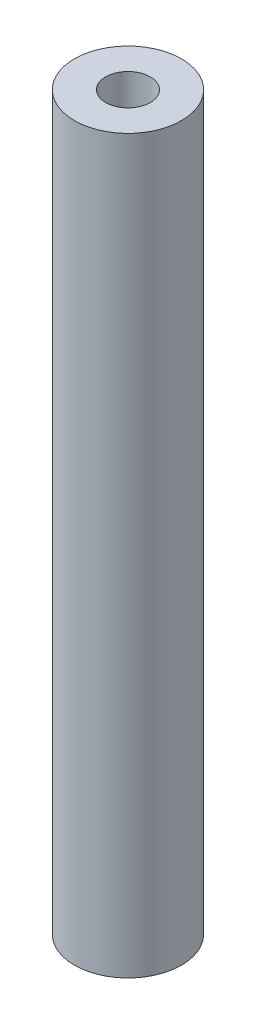
SolidWorks part; units mm, degrees
material "6061 合金"
ref_plane "前视基准面" through (0, 0, 0) normal (0, 0, 1) x (1, 0, 0)
ref_plane "上视基准面" through (0, 0, 0) normal (0, 1, 0) x (1, 0, 0)
ref_plane "右视基准面" through (0, 0, 0) normal (1, 0, 0) x (0, 0, -1)
sketch "草图1" plane through (0, 0, 0) normal (0, 1, 0) x (1, 0, 0)
  circle A0 centre (0, 0) radius 3
  dimension "D1" = 6
extrude "凸台-拉伸1" add sketch "草图1" along normal blind 41
sketch "草图2" plane through (0, 41, 0) normal (0, 1, 0) x (1, 0, 0)
  point P0 (0, 0)
hole_wizard "M3 螺纹孔1" positions "3D草图2" profile "草图3" tap size "M3" standard "GB"
sketch3d "3D草图2"
  point P0 (0, 41, 0)
sketch "草图3" plane through (0, 41, 0) normal (1, 0, 0) x (0, 0, 1)
  line L0 (0, 0) -> (0, 9.2511)
  line L1 (0, 9.2511) -> (1.25, 8.5)
  line L2 (1.25, 8.5) -> (1.25, 0)
  line L5 (1.25, 0) -> (0, 0)
  line L10 (0, 9.2511) -> (-1.25, 8.5) construction
  line L11 (0, -6.35) -> (0, 107.95) construction
  dimension "螺纹孔钻头直径" = 2.5
  dimension "螺纹孔钻头深度" = 8.5
  dimension "导头角度" = 118
cosmetic thread "孔螺蚊线1" parameters "D1"=6, "D2"=3
sketch "草图4" plane through (0, 0, 0) normal (0, -1, 0) x (1, 0, 0)
  point P0 (0, 0)
hole_wizard "M3 螺纹孔2" positions "3D草图3" profile "草图5" tap size "M3" standard "GB"
sketch3d "3D草图3"
  point P0 (0, 0, 0)
  point P3 (0, 0, 0)
sketch "草图5" plane through (0, 0, 0) normal (1, 0, 0) x (0, 0, -1)
  line L0 (0, 0) -> (0, 9.2511)
  line L1 (0, 9.2511) -> (1.25, 8.5)
  line L2 (1.25, 8.5) -> (1.25, 0)
  line L5 (1.25, 0) -> (0, 0)
  line L10 (0, 9.2511) -> (-1.25, 8.5) construction
  line L11 (0, -6.35) -> (0, 107.95) construction
  dimension "螺纹孔钻头直径" = 2.5
  dimension "螺纹孔钻头深度" = 8.5
  dimension "导头角度" = 118
cosmetic thread "孔螺蚊线2" parameters "D1"=6, "D2"=3
cosmetic thread "孔螺蚊线3" parameters "D1"=6, "D2"=3
